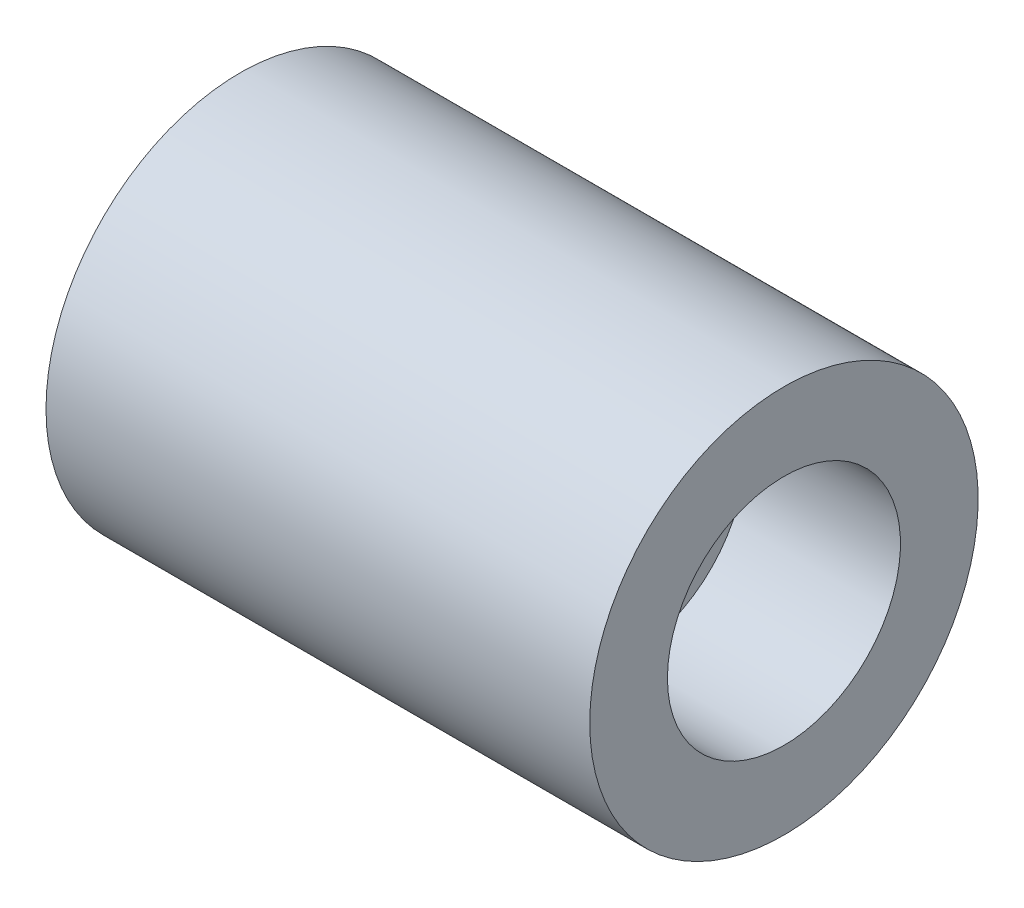
SolidWorks part; units mm, degrees
material "AISI 1020"
ref_plane "Front Plane" through (0, 0, 0) normal (0, 0, 1) x (1, 0, 0)
ref_plane "Top Plane" through (0, 0, 0) normal (0, 1, 0) x (1, 0, 0)
ref_plane "Right Plane" through (0, 0, 0) normal (1, 0, 0) x (0, 0, -1)
sketch "Sketch1" plane through (0, 0, 0) normal (0, 0, 1) x (1, 0, 0)
  line L0 (-155.2285, 0) -> (282.9589, 0) construction
  line L1 (0, 0) -> (0, 10)
  line L2 (0, 10) -> (80, 10)
  line L3 (80, 10) -> (80, 30)
  line L4 (80, 30) -> (120, 30)
  line L5 (120, 30) -> (120, 0)
  line L6 (-20, 0) -> (-20, 50)
  line L7 (-20, 50) -> (120, 50)
  line L8 (120, 50) -> (120, 30)
  dimension "D1" = 10
  dimension "D2" = 30
  dimension "D3" = 120
  dimension "D4" = 40
  dimension "D5" = 140
  dimension "D6" = 50
revolve "Revolve4" add sketch "Sketch1" angle 360 about L0
